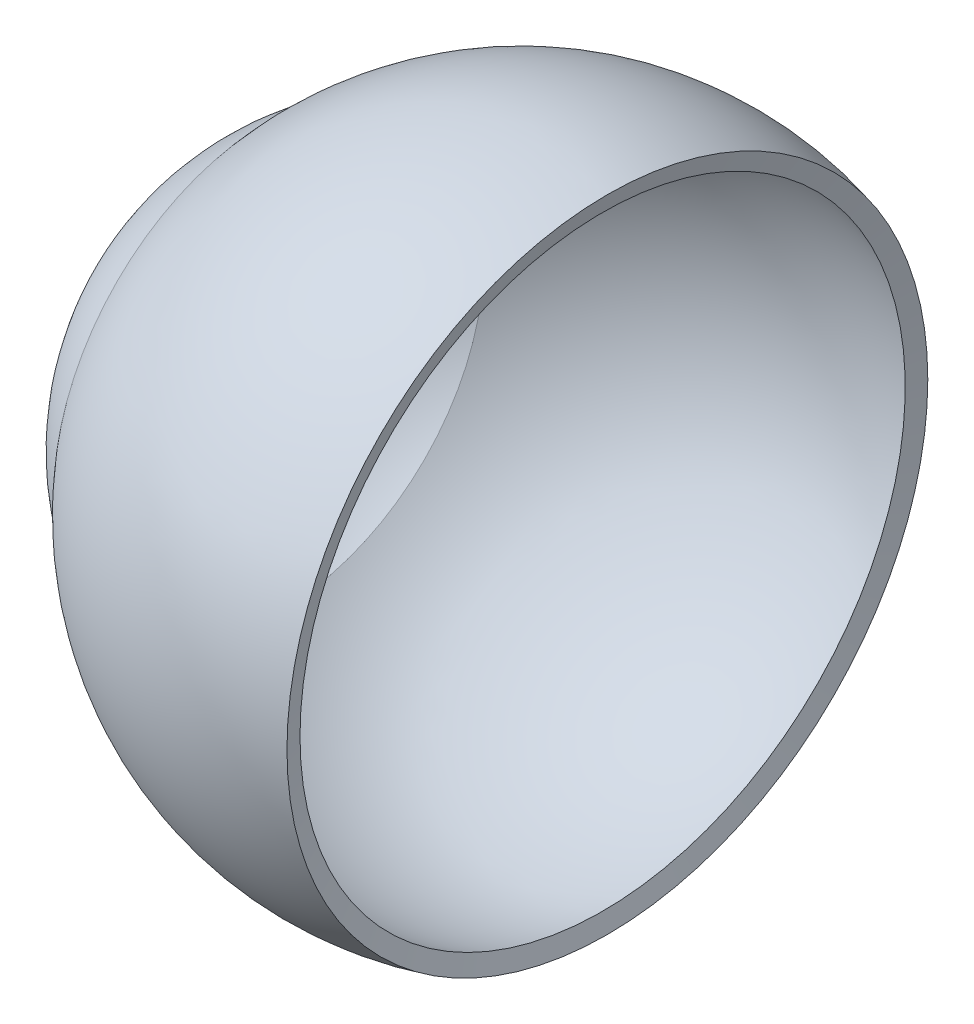
SolidWorks part; units mm, degrees
ref_plane "Front Plane" through (0, 0, 0) normal (0, 0, 1) x (1, 0, 0)
ref_plane "Top Plane" through (0, 0, 0) normal (0, 1, 0) x (1, 0, 0)
ref_plane "Right Plane" through (0, 0, 0) normal (1, 0, 0) x (0, 0, -1)
sketch "Sketch1" plane through (0, 0, 0) normal (0, 0, 1) x (1, 0, 0)
  line L0 (-10, 0) -> (0, 0) construction
  line L1 (-6.8333, 5.8571) -> (0, 0) construction
  line L2 (0, 0) -> (2.3294, 8.6933) construction
  line L3 (-9.5, 0) -> (-10, 0)
  line L4 (2.3294, 8.6933) -> (2.2, 8.2104)
  arc A0 (2.3294, 8.6933) -> (-6.8333, 5.8571) centre (0, 0) ccw
  arc A1 (-6.8333, 5.8571) -> (-10, 0) centre (-3, 0) ccw
  arc A2 (2.2, 8.2104) -> (-6.5, 5.4772) centre (0, 0) ccw
  arc A3 (-6.5, 5.4772) -> (-9.5, 0) centre (-3, 0) ccw
  dimension "D2" = 18
  dimension "D3" = 14
  dimension "D1" = 3
  dimension "D4" = 75
  dimension "D5" = 0.5
revolve "Revolve1" add sketch "Sketch1" angle 360 about L0
